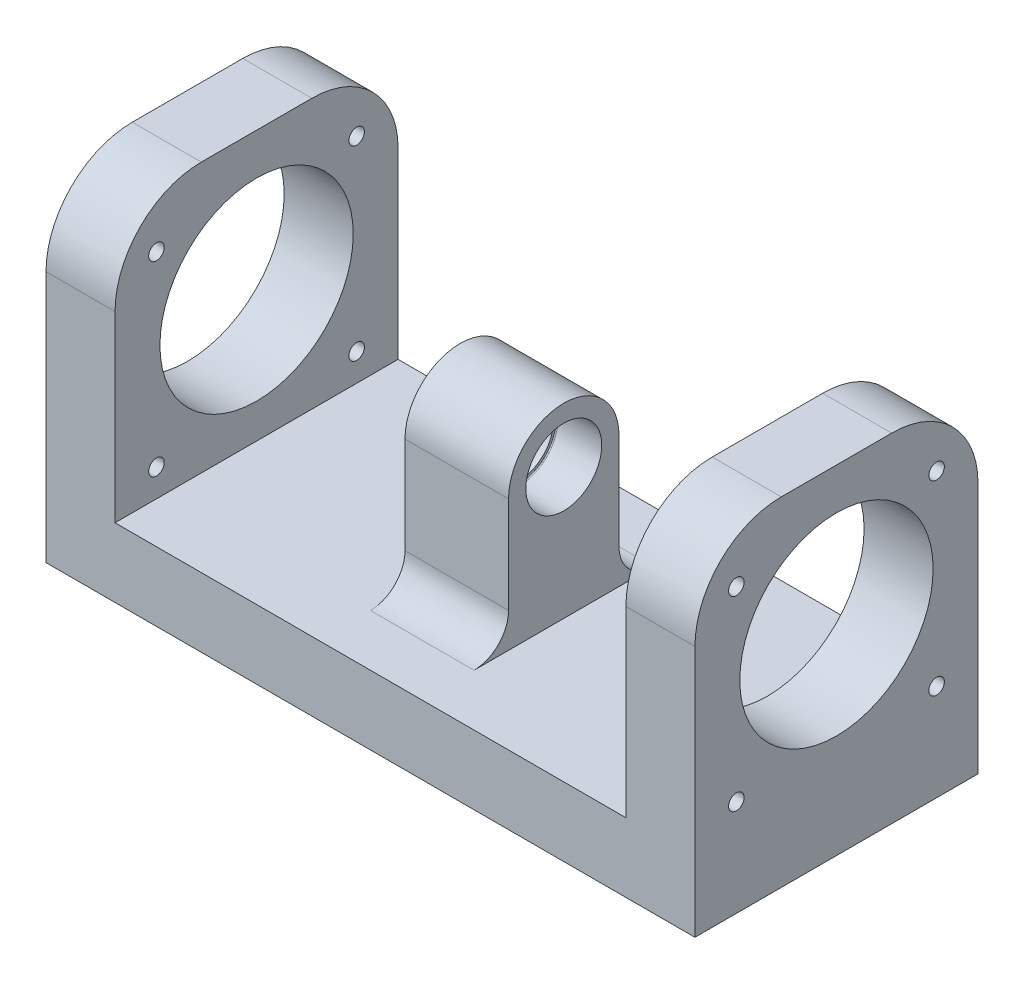
SolidWorks part; units mm, degrees
material "1060 Alloy"
ref_plane "Front Plane" through (0, 0, 0) normal (0, 0, 1) x (1, 0, 0)
ref_plane "Top Plane" through (0, 0, 0) normal (0, 1, 0) x (1, 0, 0)
ref_plane "Right Plane" through (0, 0, 0) normal (1, 0, 0) x (0, 0, -1)
sketch "Sketch1" plane through (0, 0, 0) normal (0, 0, 1) x (1, 0, 0)
  line L0 (0, 0) -> (-74, 0)
  line L1 (55, 0) -> (-55, 0) construction
  line L3 (-94, 0) -> (-94, 98)
  line L4 (-94, 98) -> (-74, 98)
  line L5 (-74, 98) -> (-74, 20)
  line L7 (-74, 20) -> (-15, 20)
  line L9 (-15, 20) -> (-15, 74)
  line L10 (-15, 74) -> (0, 74)
  line L11 (0, -55) -> (0, 55) construction
  line L12 (0, 74) -> (0, 0)
  line L13 (-94, 0) -> (-74, 0)
  dimension "D1" = 15
  dimension "D2" = 54
  dimension "D4" = 94
  dimension "D5" = 20
  dimension "D6" = 20
  dimension "D8" = 24
extrude "Boss-Extrude1" add sketch "Sketch1" against normal blind 82
sketch "Sketch5" plane through (-15, 0, 0) normal (-1, 0, 0) x (0, 0, 1)
  line L0 (-82, 74) -> (0, 74) construction
  line L1 (0, 74) -> (0, 20) construction
  circle A0 centre (-41, 58) radius 11
  dimension "D3" = 22
  dimension "D1" = 16
  dimension "D2" = 41
extrude "Cut-Extrude1" cut sketch "Sketch5" against normal blind 13
sketch "Sketch6" plane through (-2, 0, 0) normal (-1, 0, 0) x (0, 0, 1)
  circle A0 centre (-41, 58) radius 10
  dimension "D1" = 20
extrude "Cut-Extrude2" cut sketch "Sketch6" against normal up to next
fillet "Fillet1" radius 0.3 1 edges at (-2, 47, -41)
sketch "Sketch8" plane through (-74, 0, 0) normal (1, 0, 0) x (0, 0, -1)
  circle A0 centre (41, 58) radius 28
  circle A1 centre (41, 58) radius 10 construction
  dimension "D1" = 56
extrude "Cut-Extrude4" cut sketch "Sketch8" against normal up to next
sketch "Sketch10" plane through (0, 0, 0) normal (1, 0, 0) x (0, 0, -1)
  line L1 (0, 55) -> (0, -55) construction
  line L2 (82, 0) -> (82, 74) construction
  line L5 (0, 20) -> (0, 74)
  line L6 (82, 74) -> (0, 74) construction
  line L7 (0, 74) -> (82, 74)
  line L8 (82, 74) -> (82, 20)
  line L10 (25, 58) -> (25, 20)
  line L11 (25, 20) -> (57, 20)
  line L12 (57, 20) -> (57, 58)
  line L13 (82, 0) -> (0, 0) construction
  line L14 (25, 20) -> (0, 20)
  line L15 (0, 74) -> (82, 74)
  line L16 (82, 20) -> (57, 20)
  arc A0 (25, 58) -> (57, 58) centre (41, 58) cw
  point P18 (41, 74)
  dimension "D2" = 16
  dimension "D1" = 20
extrude "Cut-Extrude5" cut sketch "Sketch10" against normal up to next
fillet "Fillet3" radius 25 2 edges at (-84, 98, -82) (-84, 98, 0)
fillet "Fillet7" radius 10 2 edges at (-7.5, 20, -57) (-7.5, 20, -25)
sketch "Sketch16" plane through (0, 0, 0) normal (0, -1, 0) x (1, 0, 0)
  line L0 (0, -82) -> (0, 0) construction
  line L3 (0, -9.457) -> (0, -14.457)
  line L4 (0, -72.543) -> (0, -67.543)
  arc A0 (0, -14.457) -> (0, -67.543) centre (0, -41) ccw
  arc A2 (0, -9.457) -> (0, -72.543) centre (0, -41) ccw
  dimension "D1" = 26.543
  dimension "D2" = 5
extrude "Cut-Extrude7" cut sketch "Sketch16" against normal blind 10
hole_wizard "M4 Clearance Hole2" positions "Sketch18" profile "Sketch19" hole size "M4" standard "ANSI Metric"
sketch "Sketch18" plane through (0, 0, 0) normal (0, -1, 0) x (-1, 0, 0)
  line L0 (0, 67.543) -> (0, 14.457) construction
  line L2 (0, 82) -> (0, 72.543) construction
  arc A1 (0, 72.543) -> (0, 9.457) centre (0, 41) cw
  arc A2 (0, 9.457) -> (0, 72.543) centre (0, 41) ccw construction
  point P0 (40, 9.457)
  point P2 (40, 72.543)
  dimension "D1" = 40
sketch "Sketch19" plane through (-40, 0, -9.457) normal (1, 0, 0) x (0, 0, -1)
  line L0 (0, 0) -> (0, 11.3519)
  line L1 (0, 11.3519) -> (2.25, 10)
  line L2 (2.25, 10) -> (2.25, 0)
  line L5 (2.25, 0) -> (0, 0)
  line L10 (0, 11.3519) -> (-2.25, 10) construction
  line L11 (0, -6.35) -> (0, 107.95) construction
  dimension "Hole Dia." = 4.5
  dimension "Hole Depth" = 10
  dimension "Drill Angle" = 118
hole_wizard "M4 Clearance Hole3" positions "Sketch20" profile "Sketch21" hole size "M4" standard "ANSI Metric" end condition up to next
sketch "Sketch20" plane through (-94, 0, 0) normal (-1, 0, 0) x (0, 0, 1)
  line L0 (0, 73) -> (0, 0) construction
  line L1 (-82, 73) -> (-82, 0) construction
  line L2 (-57, 98) -> (-25, 98) construction
  line L3 (-82, 0) -> (0, 0) construction
  point P0 (-70, 28)
  point P2 (-12, 28)
  point P4 (-12, 82)
  point P6 (-70, 82)
  dimension "D1" = 12
  dimension "D2" = 12
  dimension "D3" = 16
  dimension "D4" = 28
sketch "Sketch21" plane through (-94, 28, -70) normal (0, 1, 0) x (0, 0, 1)
  line L0 (0, 0) -> (0, 20)
  line L1 (0, 20) -> (2.25, 20)
  line L2 (2.25, 20) -> (2.25, 0)
  line L5 (2.25, 0) -> (0, 0)
  line L11 (0, -6.35) -> (0, 107.95) construction
  dimension "Thru Hole Dia." = 4.5
  dimension "Thru Hole Depth" = 20
mirror "Mirror1" about plane through (0, 74, -82) normal (1, 0, 0) of bodies 114
